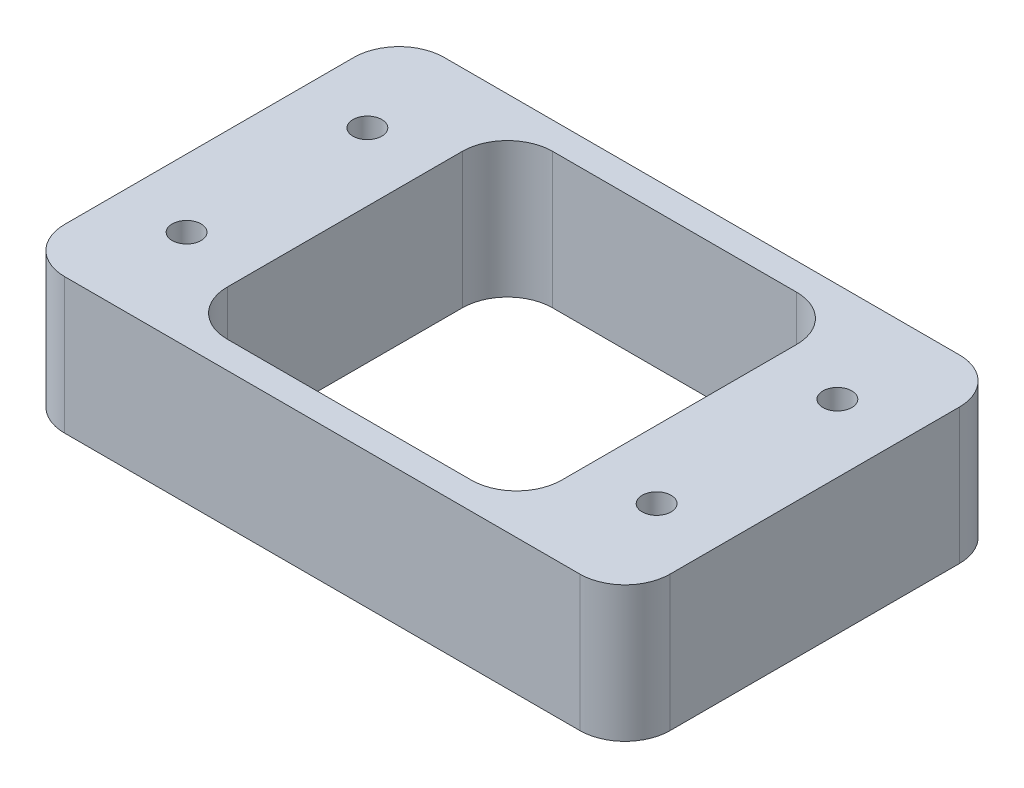
SolidWorks part; units mm, degrees
material "ABS"
ref_plane "Front Plane" through (0, 0, 0) normal (0, 0, 1) x (1, 0, 0)
ref_plane "Top Plane" through (0, 0, 0) normal (0, 1, 0) x (1, 0, 0)
ref_plane "Right Plane" through (0, 0, 0) normal (1, 0, 0) x (0, 0, -1)
sketch "Sketch1" plane through (0, 0, 0) normal (0, 1, 0) x (1, 0, 0)
  line L0 (7.5, 42) -> (7.5, 0) construction
  line L1 (0, 0) -> (67, 0)
  line L2 (0, 0) -> (0, 42)
  line L3 (0, 42) -> (67, 42)
  line L4 (67, 0) -> (67, 42)
  line L5 (33.5, 42) -> (33.5, 0) construction
  line L6 (67, 21) -> (0, 21) construction
  circle A0 centre (7.5, 31) radius 1.6
  circle A1 centre (7.5, 11) radius 1.6
  circle A2 centre (59.5, 11) radius 1.6
  circle A3 centre (59.5, 31) radius 1.6
  dimension "D3" = 20
  dimension "D4" = 3.2
  dimension "D1" = 67
  dimension "D2" = 42
  dimension "D5" = 7.5
extrude "Boss-Extrude1" add sketch "Sketch1" along normal blind 15
sketch "Sketch2" plane through (0, 15, 0) normal (0, 1, 0) x (1, 0, 0)
  line L0 (67, 42) -> (0, 42) construction
  line L5 (0, 21) -> (67, 21) construction
  line L6 (0, 42) -> (0, 0) construction
  line L7 (67, 0) -> (67, 42) construction
  line L8 (15, 3) -> (52, 3)
  line L9 (15, 3) -> (15, 39)
  line L10 (15, 39) -> (52, 39)
  line L11 (52, 3) -> (52, 39)
  line L12 (15, 3) -> (52, 39) construction
  line L13 (15, 39) -> (52, 3) construction
  point P0 (33.5, 21)
  dimension "D1" = 3
  dimension "D2" = 15
extrude "Cut-Extrude1" cut sketch "Sketch2" against normal through all
fillet "Fillet1" radius 5 8 edges at (0, 7.5, -42) (67, 7.5, -42) (67, 7.5, 0) (0, 7.5, 0) (52, 7.5, -3) (15, 7.5, -39) (52, 7.5, -39) (15, 7.5, -3)
